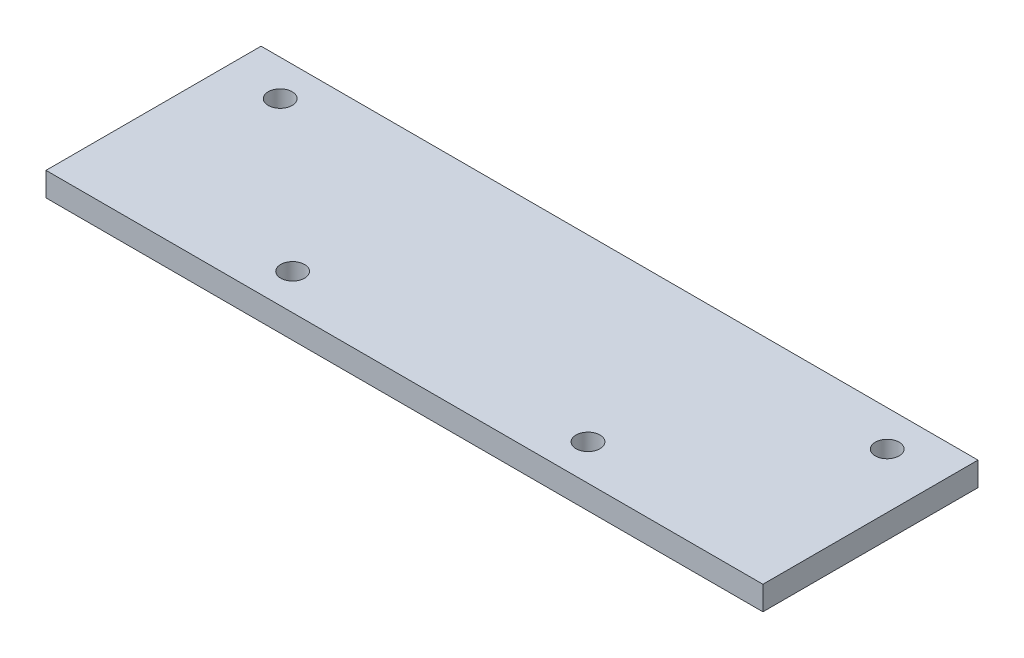
SolidWorks part; units mm, degrees
material "1060 Alloy"
ref_plane "Front Plane" through (0, 0, 0) normal (0, 0, 1) x (1, 0, 0)
ref_plane "Top Plane" through (0, 0, 0) normal (0, 1, 0) x (1, 0, 0)
ref_plane "Right Plane" through (0, 0, 0) normal (1, 0, 0) x (0, 0, -1)
sketch "Sketch1" plane through (0, 0, 0) normal (0, 1, 0) x (1, 0, 0)
  line L1 (-95.25, 28.575) -> (95.25, 28.575)
  line L2 (-95.25, 28.575) -> (-95.25, -28.575)
  line L3 (-95.25, -28.575) -> (95.25, -28.575)
  line L4 (95.25, 28.575) -> (95.25, -28.575)
  line L5 (-95.25, 28.575) -> (95.25, -28.575) construction
  line L6 (-95.25, -28.575) -> (95.25, 28.575) construction
  point P0 (0, 0)
  dimension "D1" = 190.5
  dimension "D2" = 57.15
extrude "Boss-Extrude1" add sketch "Sketch1" along normal blind 6.35
sketch "Sketch3" plane through (0, 0, 0) normal (0, -1, 0) x (1, 0, 0)
  line L0 (-95.25, -28.575) -> (-95.25, 28.575) construction
  line L1 (95.25, -28.575) -> (-95.25, -28.575) construction
  circle A0 centre (-80.645, -19.05) radius 3.175
  circle A1 centre (-39.243, 19.05) radius 3.175
  dimension "D3" = 6.35
  dimension "D6" = 6.35
  dimension "D1" = 14.605
  dimension "D2" = 9.525
  dimension "D4" = 47.625
  dimension "D5" = 56.007
extrude "Cut-Extrude2" cut sketch "Sketch3" against normal through all
mirror "Mirror1" about plane through (0, 0, 0) normal (1, 0, 0) of "Cut-Extrude2"
